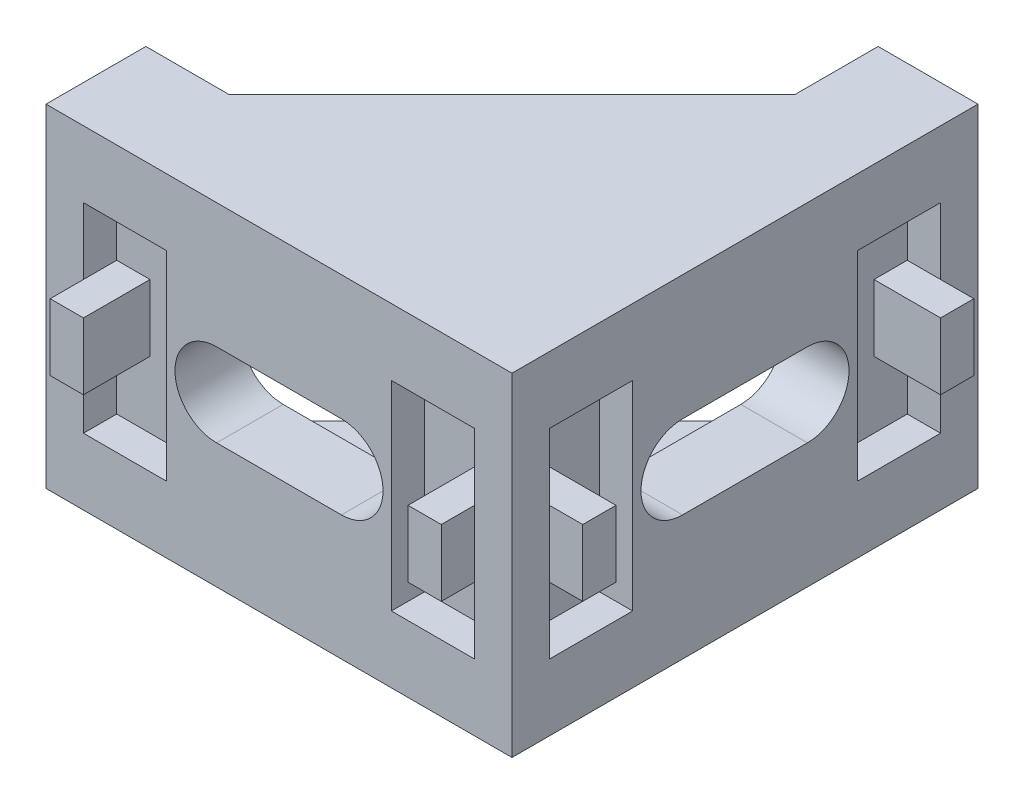
SolidWorks part; units mm, degrees
material "1060 Alloy"
ref_plane "Front Plane" through (0, 0, 0) normal (0, 0, 1) x (1, 0, 0)
ref_plane "Top Plane" through (0, 0, 0) normal (0, 1, 0) x (1, 0, 0)
ref_plane "Right Plane" through (0, 0, 0) normal (1, 0, 0) x (0, 0, -1)
sketch "Sketch1" plane through (0, 0, 0) normal (0, 1, 0) x (1, 0, 0)
  line L0 (-28, 0) -> (0, 0)
  line L1 (0, 0) -> (0, 28)
  line L2 (0, 28) -> (-6, 28)
  line L3 (-6, 28) -> (-6, 23)
  line L4 (-6, 23) -> (-23, 6)
  line L5 (-23, 6) -> (-28, 6)
  line L6 (-28, 6) -> (-28, 0)
  dimension "D1" = 28
  dimension "D2" = 28
  dimension "D3" = 6
  dimension "D4" = 6
  dimension "D5" = 5
  dimension "D6" = 5
extrude "Boss-Extrude1" add sketch "Sketch1" along normal blind 20
sketch "Sketch2" plane through (0, 0, -28) normal (0, 0, -1) x (-1, 0, 0)
  line L0 (0, 0) -> (6, 0) construction
  line L1 (4, 17) -> (28, 17)
  line L2 (4, 17) -> (4, 3)
  line L3 (4, 3) -> (28, 3)
  line L4 (28, 17) -> (28, 3)
  line L5 (6, 20) -> (23, 20) construction
  line L6 (6, 20) -> (6, 0) construction
  line L7 (23, 20) -> (23, 0) construction
  dimension "D1" = 3
  dimension "D2" = 3
  dimension "D3" = 2
  dimension "D4" = 5
extrude "Cut-Extrude1" cut sketch "Sketch2" against normal blind 24
sketch "Sketch3" plane through (0, 0, 0) normal (0, 0, 1) x (1, 0, 0)
  line L0 (-28, 20) -> (-28, 0) construction
  line L1 (-25.75, 4) -> (-20.75, 4)
  line L2 (-25.75, 4) -> (-25.75, 16)
  line L3 (-25.75, 16) -> (-20.75, 16)
  line L4 (-20.75, 4) -> (-20.75, 16)
  line L5 (-28, 20) -> (0, 20) construction
  line L6 (-28, 0) -> (0, 0) construction
  line L7 (-14, 20) -> (-14, 0) construction
  line L8 (-7.25, 4) -> (-7.25, 16)
  line L9 (-2.25, 16) -> (-7.25, 16)
  line L10 (-2.25, 4) -> (-2.25, 16)
  line L11 (-2.25, 4) -> (-7.25, 4)
  dimension "D1" = 2.25
  dimension "D2" = 4
  dimension "D3" = 4
  dimension "D4" = 5
extrude "Cut-Extrude2" cut sketch "Sketch3" against normal blind 2
sketch "Sketch4" plane through (0, 0, -2) normal (0, 0, 1) x (1, 0, 0)
  line L0 (-25.75, 16) -> (-25.75, 4) construction
  line L1 (-25.75, 12) -> (-23.75, 12)
  line L2 (-25.75, 12) -> (-25.75, 8)
  line L3 (-25.75, 8) -> (-23.75, 8)
  line L4 (-23.75, 12) -> (-23.75, 8)
  line L5 (-20.75, 16) -> (-25.75, 16) construction
  line L6 (-14, 20) -> (-14, 0) construction
  line L7 (-28, 20) -> (0, 20) construction
  line L8 (-28, 0) -> (0, 0) construction
  line L9 (-4.25, 12) -> (-4.25, 8)
  line L10 (-2.25, 8) -> (-4.25, 8)
  line L11 (-2.25, 12) -> (-2.25, 8)
  line L12 (-2.25, 12) -> (-4.25, 12)
  dimension "D1" = 2
  dimension "D2" = 4
  dimension "D3" = 4
extrude "Boss-Extrude2" add sketch "Sketch4" along normal blind 4
ref_plane "Plane5" through (0, 0, 0) normal (-0.7071, 0, 0.7071) x (0.7071, 0, 0.7071)
mirror "Mirror11" about plane through (0, 0, 0) normal (-0.7071, 0, 0.7071) of "Cut-Extrude2", "Boss-Extrude2"
sketch "Sketch5" plane through (0, 0, -4) normal (0, 0, -1) x (-1, 0, 0)
  line L0 (10.25, 10) -> (17.75, 10) construction
  line L1 (10.25, 12.5) -> (17.75, 12.5)
  line L2 (10.25, 7.5) -> (17.75, 7.5)
  line L4 (28, 3) -> (28, 17) construction
  arc A0 (10.25, 12.5) -> (10.25, 7.5) centre (10.25, 10) ccw
  arc A1 (17.75, 7.5) -> (17.75, 12.5) centre (17.75, 10) ccw
  point P2 (14, 10)
  dimension "D1" = 2.5
  dimension "D3" = 17.75
  dimension "D2" = 7.5
extrude "Cut-Extrude3" cut sketch "Sketch5" against normal up to next (4 mm away)
mirror "Mirror12" about plane through (0, 0, 0) normal (-0.7071, 0, 0.7071) of "Cut-Extrude3"
